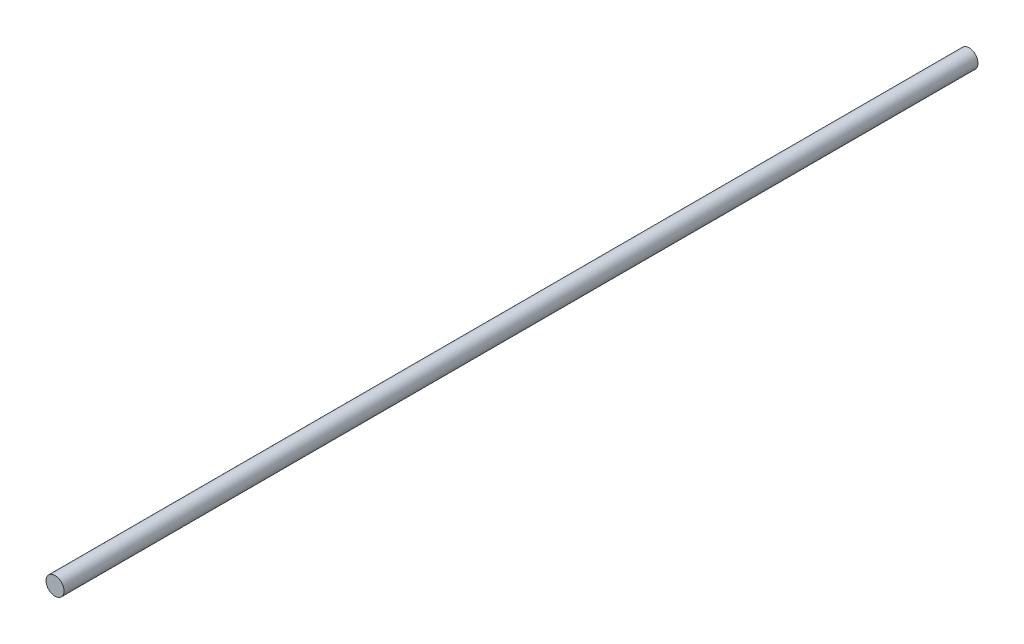
SolidWorks part; units mm, degrees
material "Plain Carbon Steel"
ref_plane "Front Plane" through (0, 0, 0) normal (0, 0, 1) x (1, 0, 0)
ref_plane "Top Plane" through (0, 0, 0) normal (0, 1, 0) x (1, 0, 0)
ref_plane "Right Plane" through (0, 0, 0) normal (1, 0, 0) x (0, 0, -1)
sketch "Sketch1" plane through (0, 0, 0) normal (0, 1, 0) x (1, 0, 0)
  line L0 (0, 0) -> (0, -31.319) construction
  line L2 (0, 0) -> (4, 0)
  line L3 (0, 0) -> (0, 406)
  line L4 (0, 406) -> (4, 406)
  line L5 (4, 0) -> (4, 406)
  dimension "D1" = 8
  dimension "D2" = 406
revolve "Revolve1" add sketch "Sketch1" angle 360 about L0
